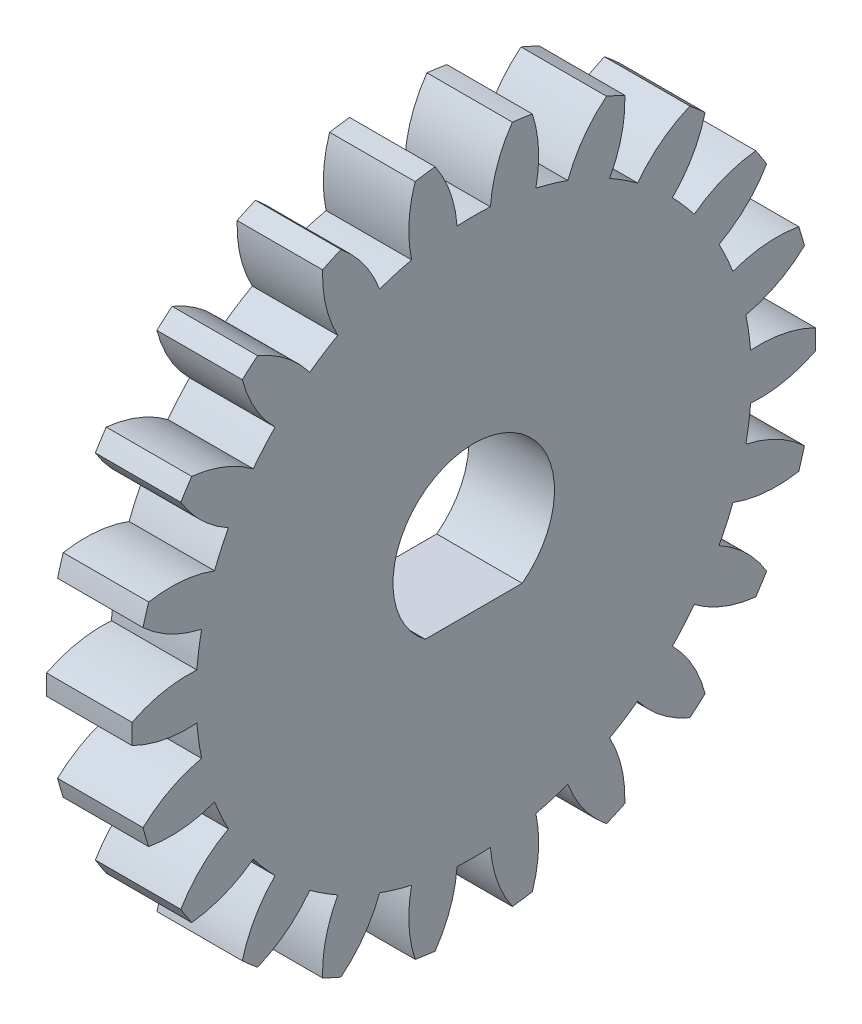
SolidWorks part; units mm, degrees
ref_plane "Plane1" through (0, 0, 0) normal (0, 0, 1) x (1, 0, 0)
ref_plane "Plane2" through (0, 0, 0) normal (0, 1, 0) x (1, 0, 0)
ref_plane "Plane3" through (0, 0, 0) normal (1, 0, 0) x (0, 0, -1)
sketch "HoldingSke" plane through (0, 0, 0) normal (0, 1, 0) x (1, 0, 0)
  line L0 (0, 0) -> (565.2113, -228.3602)
  line L1 (-15, 0) -> (100, 0) construction
  line L2 (0, 0) -> (-2.1039, 2.3779)
  line L3 (0, 0) -> (-11.863, 4.5341)
  line L4 (0, 0) -> (8.0072, 3.2351)
  line L5 (0, 0) -> (-47.5972, -17.7524)
  line L6 (0, 0) -> (-2.632, -1.7758)
  line L7 (-2.1039, 2.3779) -> (8.8308, 51.9871)
  line L8 (-76.2, 54.61) -> (-71.1708, 54.61)
  line L9 (-67.7845, 28.3722) -> (-49.3413, 33.142)
  line L10 (-76.2, 71.12) -> (104.1128, 71.12)
  line L11 (0, 0) -> (-3.175, 0)
  line L12 (-76.2, 101.6) -> (-76.1573, 101.6)
  line L13 (24.9733, 27.94) -> (52.9518, 28.4284)
  line L14 (24.9733, 27.94) -> (25.0241, 27.9398)
  line L15 (24.9733, 27.94) -> (100.4021, 29.52)
  circle A0 centre (0, 0) radius 2.3813
  circle A1 centre (0, 0) radius 10.3209
  circle A2 centre (0, 0) radius 38.1
  circle A3 centre (0, 0) radius 2.3813
  dimension "MHD" = 20.6417
  dimension "Hub_dia" = 76.2
  dimension "Bore" = 4.7625
  dimension "MBD" = 4.7625
  dimension "Num_teeth" = 22
  dimension "Pitch_radius" = 180.3128
  dimension "Pitch" = 609.6
  dimension "Width" = 3.175
  dimension "Overall_len" = 50.8
  dimension "Show_teeth" = 22
  dimension "Thickness" = 3.175
  dimension "OAL" = 50.8001
  dimension "T_dim" = 5.0292
  dimension "Ap" = 14.5
  dimension "H" = 19.05
  dimension "Backlash" = 0.0427
  dimension "Addendum_fac" = 1
  dimension "Dedendum_fac" = 1.2
  dimension "Clearance_fac" = 0.2
  dimension "Dedendum_add" = 0.0508
sketch "BasProSke" plane through (0, 0, 0) normal (0, 1, 0) x (1, 0, 0)
  line L0 (-10, 0) -> (60, 0) construction
  line L1 (0, 0) -> (0, 12.7)
  line L2 (0, 0) -> (3.175, 0)
  line L3 (3.175, 0) -> (3.175, 12.7)
  line L4 (3.175, 12.7) -> (0, 12.7)
  dimension "Diameter" = 25.4
  dimension "Thickness" = 3.175
revolve "Base-Revolve" add sketch "BasProSke" angle 360 about L0
sketch "TooCutSke" plane through (0, 0, 0) normal (1, 0, 0) x (0, 0, -1)
  line L1 (0, 0) -> (0, 107) construction
  line L2 (0, 0) -> (-0.9051, 11.6064) construction
  line L3 (0, 0) -> (-3.3066, 22.9977) construction
  line L4 (-0.9051, 11.6064) -> (-1.6533, 11.4989) construction
  arc A0 (0.6189, 10.3023) -> (-0.6189, 10.3023) centre (0, 0) ccw
  arc A1 (1.4524, 12.6422) -> (-1.4524, 12.6422) centre (0, 0) ccw
  circle A2 centre (0, 0) radius 11.6417 construction
  circle A3 centre (0, 0) radius 11.2709 construction
  arc A4 (-0.6189, 10.3023) -> (-1.4524, 12.6422) centre (-5.2634, 9.9664) ccw
  arc A5 (1.4524, 12.6422) -> (0.6189, 10.3023) centre (5.2634, 9.9664) ccw
  dimension "Root_dia" = 20.6417
  dimension "Overcut_dia" = 25.4508
  dimension "Pitch_dia" = 23.2833
  dimension "Base_dia" = 22.5417
  dimension "Flank_rad" = 4.6567
  dimension "Half_ang" = 8.182
  dimension "Half_CT" = 0.7558
extrude "ToothCut" cut sketch "TooCutSke" along normal through all
fillet "Breaks" [suppressed] radius 0.0212
fillet "RootFillets" [suppressed] radius 0.2625
pattern_circular "TeethCuts" count 22 every 16.364 about axis through (-10, 0, 0) along (1, 0, 0) of "ToothCut", "RootFillets", "Breaks"
sketch "HubNeaOneSke" plane through (0, 0, 0) normal (-1, 0, 0) x (0, 0, 1)
  circle A0 centre (0, 0) radius 10.3209
  dimension "Diameter" = 20.6417
extrude "HubNearOne" [suppressed] add sketch "HubNeaOneSke" along normal blind 47.6251
sketch "HubNeaBotSke" plane through (0, 0, 0) normal (-1, 0, 0) x (0, 0, 1)
  circle A0 centre (0, 0) radius 10.3209
  dimension "Diameter" = 20.6417
extrude "HubNearBoth" [suppressed] add sketch "HubNeaBotSke" along normal blind 23.8125
ref_plane "FarPln" through (3.175, 0, 0) normal (1, 0, 0) x (0, 0, -1)
sketch "HubFarSke" plane through (3.175, 0, 0) normal (1, 0, 0) x (0, 0, -1)
  circle A0 centre (0, 0) radius 10.3209
  dimension "Diameter" = 20.6417
extrude "HubFar" [suppressed] add sketch "HubFarSke" along normal blind 23.8125
sketch "BorSke" plane through (0, 0, 0) normal (1, 0, 0) x (0, 0, -1)
  circle A0 centre (0, 0) radius 2.3813
  dimension "Diameter" = 4.7625
extrude "Bore" [suppressed] cut sketch "BorSke" along normal mid plane 101.6001
sketch "KeySke" plane through (0, 0, 0) normal (1, 0, 0) x (0, 0, -1)
  line L0 (-0.127, 0) -> (-0.127, 2.6479)
  line L1 (-0.127, 2.6479) -> (0.127, 2.6479)
  line L2 (0.127, 2.6479) -> (0.127, 0)
  line L3 (0, 0) -> (0, 34) construction
  line L4 (-0.127, 0) -> (0.127, 0)
  dimension "Offset" = 2.6479
  dimension "Width" = 0.254
extrude "Keyway" [suppressed] cut sketch "KeySke" along normal mid plane 101.6001
pattern_circular "Keyway2" [suppressed] count 2 every 90 about axis through (-10, 0, 0) along (1, 0, 0)
sketch "Sketch1" plane through (3.175, 0, 0) normal (1, 0, 0) x (0, 0, -1)
  line L0 (-1.8, -2.4) -> (1.8, -2.4)
  arc A0 (1.8, -2.4) -> (-1.8, -2.4) centre (0, 0) ccw
  dimension "D1" = 6
  dimension "D2" = 5.4
extrude "Cut-Extrude1" cut sketch "Sketch1" against normal up to next
equation "' \"Pitch@HoldingSke\" = 4"
equation "' \"Num_teeth@HoldingSke\" = 12"
equation "' \"Ap@HoldingSke\" =  20"
equation "' \"Width@HoldingSke\" = 0.5"
equation "' \"Hub_dia@HoldingSke\"= 1"
equation "' \"Overall_len@HoldingSke\" = 1.0"
equation "' \"Bore@HoldingSke\" = 0.75"
equation "' \"T_dim@HoldingSke\" = 0.85"
equation "' \"Width@KeySke\" = 0.25"
equation "' \"Show_teeth@HoldingSke\" = 13"
equation "' \"Backlash@HoldingSke\" = 0.009"
equation "' \"Addendum_fac@HoldingSke\" = 1.0"
equation "' \"Dedendum_fac@HoldingSke\" = 1.25"
equation "' \"Dedendum_add@HoldingSke\" = 0.00005"
equation "' \"Clearance_fac@HoldingSke\" = 0.25"
equation "' \"Pitch@HoldingSke\" = 0.5"
equation "' \"Num_teeth@HoldingSke\" = 23"
equation "' \"Show_teeth@HoldingSke\" = 23"
equation "' \"Backlash@HoldingSke\" = 0.0375"
equation "\"Overcut_dia@TooCutSke\" = (\"Num_teeth@HoldingSke\" + 2 * \"Addendum_fac@HoldingSke\") / \"Pitch@HoldingSke\" + 0.002"
equation "\"Pitch_dia@TooCutSke\" = \"Num_teeth@HoldingSke\" / \"Pitch@HoldingSke\""
equation "\"Base_dia@TooCutSke\" = \"Num_teeth@HoldingSke\" / \"Pitch@HoldingSke\" * cos((\"Ap@HoldingSke\"  * 3.14159265 / 180))"
equation "\"Root_dia@TooCutSke\" = (\"Num_teeth@HoldingSke\" + 2) / \"Pitch@HoldingSke\" - 2 * (\"Addendum_fac@HoldingSke\" + \"Dedendum_fac@HoldingSke\") / \"Pitch@HoldingSke\" - \"Dedendum_add@HoldingSke\" * 2"
equation "\"Half_ang@TooCutSke\" = 180 / \"Num_teeth@HoldingSke\""
equation "\"Half_CT@TooCutSke\" = \"Num_teeth@HoldingSke\" / \"Pitch@HoldingSke\" * sin((3.14159265 / 2 / \"Num_teeth@HoldingSke\")) / 2 - 7 * \"Backlash@HoldingSke\" / 4"
equation "\"Flank_rad@TooCutSke\" = \"Num_teeth@HoldingSke\" / \"Pitch@HoldingSke\" / 5"
equation "\"Radius@RootFillets\" = \"Clearance_fac@HoldingSke\" / \"Pitch@HoldingSke\" + \"Dedendum_add@HoldingSke\""
equation "\"Break_rad@Breaks\" = 0.02 / \"Pitch@HoldingSke\""
equation "\"Thickness@HoldingSke\" = \"Width@HoldingSke\""
equation "\"OAL@HoldingSke\" = \"Thickness@HoldingSke\""
equation "\"MHD@HoldingSke\" = (\"Num_teeth@HoldingSke\" + 2) / \"Pitch@HoldingSke\" - 2 * (\"Addendum_fac@HoldingSke\" + \"Dedendum_fac@HoldingSke\")  / \"Pitch@HoldingSke\" - \"Dedendum_add@HoldingSke\" * 2"
equation "\"MBD@HoldingSke\" = (\"Num_teeth@HoldingSke\" + 2) / \"Pitch@HoldingSke\" - 2 * (\"Addendum_fac@HoldingSke\" + \"Dedendum_fac@HoldingSke\")  / \"Pitch@HoldingSke\" - \"Dedendum_add@HoldingSke\" * 2 - 0.002"
equation "\"MHD@HoldingSke\" = ((sgn( \"MHD@HoldingSke\" - \"Hub_dia@HoldingSke\" )-1)*( \"MHD@HoldingSke\" - \"Hub_dia@HoldingSke\" ))/-2+ \"Hub_dia@HoldingSke\""
equation "\"MBD@HoldingSke\" = ((sgn( \"MBD@HoldingSke\" - \"Bore@HoldingSke\" )-1)*( \"MBD@HoldingSke\" - \"Bore@HoldingSke\" ))/-2+ \"Bore@HoldingSke\""
equation "\"OAL@HoldingSke\" = ((sgn( \"OAL@HoldingSke\" - \"Overall_len@HoldingSke\" )+1)*( \"OAL@HoldingSke\" - \"Overall_len@HoldingSke\" ))/2 + \"Overall_len@HoldingSke\" + 0.000002"
equation "\"Num_teeth@TeethCuts\" = int( \"Show_teeth@HoldingSke\" ) + 1"
equation "\"Num_teeth@TeethCuts\" = ((sgn( \"Num_teeth@TeethCuts\" - \"Num_teeth@HoldingSke\" )-1)*( \"Num_teeth@TeethCuts\" - \"Num_teeth@HoldingSke\" ))/-2+ \"Num_teeth@HoldingSke\""
equation "\"Num_teeth@TeethCuts\" = ((sgn( \"Num_teeth@TeethCuts\" - 2.0)+1)*( \"Num_teeth@TeethCuts\" - 2.0))/2 +2.0"
equation "\"Angle@TeethCuts\" = 360.0 / \"Num_teeth@HoldingSke\""
equation "\"Diameter@BasProSke\" = (\"Num_teeth@HoldingSke\" + 2 * \"Addendum_fac@HoldingSke\") / \"Pitch@HoldingSke\""
equation "\"Thickness@BasProSke\"  = \"Thickness@HoldingSke\""
equation "' \"Fillet_rad@BasProSke\" =  \"Thickness@HoldingSke\" * 0.05"
equation "\"MHD@HoldingSke\" = ((sgn( \"MHD@HoldingSke\" - \"Root_dia@TooCutSke\" )-1)*( \"MHD@HoldingSke\" - \"Root_dia@TooCutSke\" ))/-2+ \"Root_dia@TooCutSke\""
equation "\"Diameter@HubNeaOneSke\" = \"MHD@HoldingSke\""
equation "\"Length@HubNearOne\" = \"OAL@HoldingSke\" - \"Thickness@BasProSke\""
equation "\"Diameter@HubNeaBotSke\" = \"MHD@HoldingSke\""
equation "\"Length@HubNearBoth\" = ( \"OAL@HoldingSke\" - \"Thickness@BasProSke\" ) / 2.0"
equation "\"Thickness@FarPln\" = \"Thickness@BasProSke\""
equation "\"Diameter@HubFarSke\" = \"MHD@HoldingSke\""
equation "\"Length@HubFar\" = ( \"OAL@HoldingSke\" - \"Thickness@BasProSke\" ) / 2.0"
equation "\"Diameter@BorSke\" = \"MBD@HoldingSke\""
equation "\"D1@Bore\" = \"OAL@HoldingSke\" * 2.0"
equation "\"D1@Keyway\" = \"OAL@HoldingSke\" * 2.0"
equation "\"Offset@KeySke\" = \"T_dim@HoldingSke\" - \"MBD@HoldingSke\" / 2.0"
